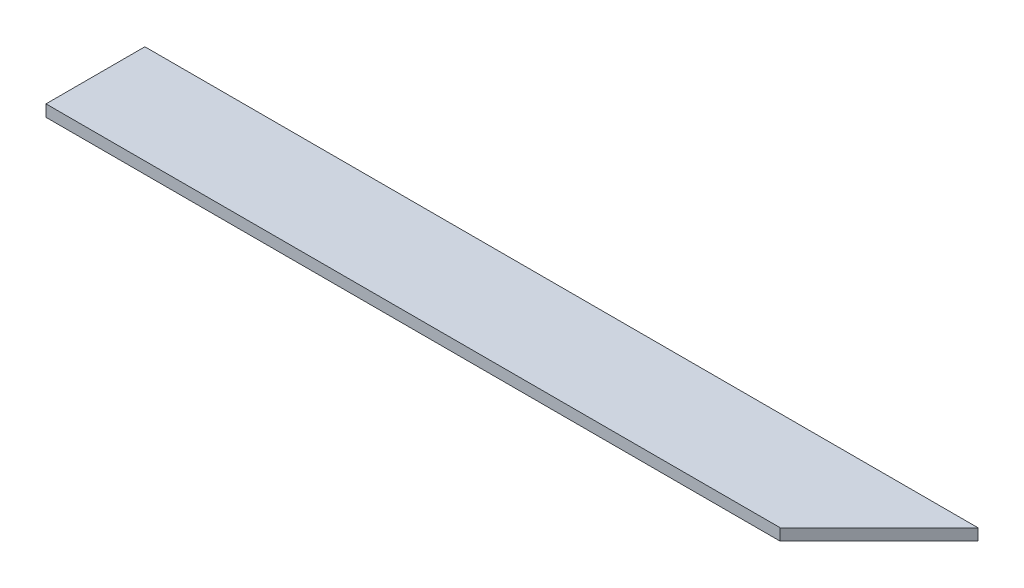
SolidWorks part; units mm, degrees
ref_plane "Front Plane" through (0, 0, 0) normal (0, 0, 1) x (1, 0, 0)
ref_plane "Top Plane" through (0, 0, 0) normal (0, 1, 0) x (1, 0, 0)
ref_plane "Right Plane" through (0, 0, 0) normal (1, 0, 0) x (0, 0, -1)
sketch "Sketch1" plane through (0, 0, 0) normal (0, 1, 0) x (1, 0, 0)
  line L1 (-99.8701, 34.921) -> (114.1299, 34.921)
  line L2 (-99.8701, 34.921) -> (-99.8701, 9.521)
  line L3 (-99.8701, 9.521) -> (114.1299, 9.521)
  line L4 (114.1299, 34.921) -> (114.1299, 9.521)
  dimension "D1" = 214
  dimension "D2" = 25.4
extrude "Boss-Extrude1" add sketch "Sketch1" along normal blind 3
sketch "Sketch2" plane through (0, 3, 0) normal (0, 1, 0) x (1, 0, 0)
  line L4 (114.1299, 34.921) -> (88.7299, 9.521)
  line L5 (-99.8701, 9.521) -> (114.1299, 9.521) construction
  line L6 (88.7299, 9.521) -> (114.1299, 9.521)
  line L7 (114.1299, 9.521) -> (114.1299, 34.921)
extrude "Cut-Extrude2" cut sketch "Sketch2" against normal blind 10
